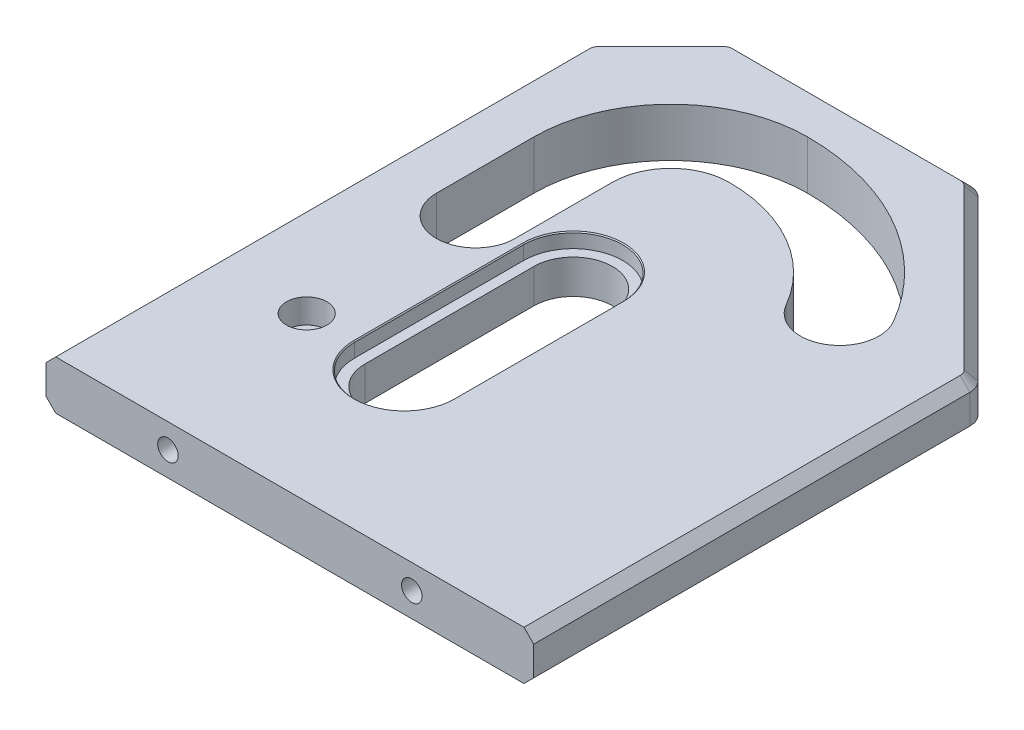
SolidWorks part; units mm, degrees
ref_plane "Front Plane" through (0, 0, 0) normal (0, 0, 1) x (1, 0, 0)
ref_plane "Top Plane" through (0, 0, 0) normal (0, 1, 0) x (1, 0, 0)
ref_plane "Right Plane" through (0, 0, 0) normal (1, 0, 0) x (0, 0, -1)
sketch "Sketch1" plane through (0, 0, 0) normal (0, 1, 0) x (1, 0, 0)
  line L1 (-40, -68.0944) -> (60, -68.0944)
  line L2 (-40, -68.0944) -> (-40, 58)
  line L3 (-40, 58) -> (60, 58)
  line L4 (60, -68.0944) -> (60, 58)
  dimension "D1" = 68.0944
  dimension "D2" = 40
  dimension "D3" = 58
  dimension "D4" = 60
extrude "Boss-Extrude1" add sketch "Sketch1" along normal mid plane 10
sketch "Slots Path" plane through (0, 0, 0) normal (0, 1, 0) x (1, 0, 0)
  line L2 (-20, 0) -> (-20, 20)
  line L3 (0, 0) -> (0, -34.641)
  line L4 (-5.5, 0) -> (5.5, 0) construction
  arc A1 (0, 40) -> (-20, 20) centre (0, 20) ccw
  arc A2 (0, 40) -> (34.641, 20) centre (0, 0) cw
  point P1 (-20, -34.641)
  dimension "D1" = 20
  dimension "D2" = 40
  dimension "D3" = 20
  dimension "D4" = 20
  dimension "D5" = 40
sketch "Sketch3" plane through (0, 5, 0) normal (0, 1, 0) x (1, 0, 0)
  line L9 (-8.05, 0) -> (-8.05, -34.641)
  line L10 (-11.95, 0) -> (-11.95, 20)
  line L11 (-28.05, 0) -> (-28.05, 20)
  line L12 (8.05, 0) -> (8.05, -34.641)
  arc A2 (-8.05, 0) -> (8.05, 0) centre (0, 0) cw
  arc A3 (-8.05, -34.641) -> (8.05, -34.641) centre (0, -34.641) ccw
  arc A18 (0, 31.95) -> (-11.95, 20) centre (0, 20) ccw
  arc A19 (27.6695, 15.975) -> (0, 31.95) centre (0, 0) ccw
  arc A20 (0, 48.05) -> (-28.05, 20) centre (0, 20) ccw
  arc A21 (41.6125, 24.025) -> (0, 48.05) centre (0, 0) ccw
  arc A22 (-11.95, 0) -> (-28.05, 0) centre (-20, 0) cw
  arc A23 (27.6695, 15.975) -> (41.6125, 24.025) centre (34.641, 20) ccw
extrude "Slots" cut sketch "Sketch3" against normal through all
sketch "Sketch11" plane through (0, 5, 0) normal (0, 1, 0) x (1, 0, 0)
  line L4 (-10.15, 0) -> (-10.15, -34.641)
  line L5 (10.15, 0) -> (10.15, -34.641)
  arc A2 (-10.15, 0) -> (10.15, 0) centre (0, 0) cw
  arc A3 (-10.15, -34.641) -> (10.15, -34.641) centre (0, -34.641) ccw
extrude "Cut-Extrude5" cut sketch "Sketch11" against normal blind 3
chamfer "Chamfer2" distance 0.2 angle 45 4 edges at (0, 5, 44.791) (10.15, 5, 17.3205) (0, 5, -10.15) (-10.15, 5, 17.3205)
hole_wizard "M5x0.8 Tapped Hole2" positions "Sketch8" profile "Sketch9" tap size "M5x0.8" standard "ANSI Metric" end condition through all
sketch "Sketch8" plane through (0, 5, 0) normal (0, 1, 0) x (1, 0, 0)
  point P0 (-20, -34.641)
cosmetic thread "Hole Thread3" parameters "D2"=5
sketch "Sketch9" plane through (-20, 5, 34.641) normal (1, 0, 0) x (0, 0, 1)
  line L0 (0, 0) -> (0, 10)
  line L1 (0, 10) -> (2.1, 10)
  line L2 (2.1, 10) -> (2.1, 0)
  line L5 (2.1, 0) -> (0, 0)
  line L11 (0, -6.35) -> (0, 107.95) construction
  dimension "Thru Tap Drill Dia." = 4.2
  dimension "Thru Tap Drill Depth" = 10
sketch "Sketch10" plane through (0, 5, 0) normal (0, 1, 0) x (1, 0, 0)
  circle A0 centre (-20, -34.641) radius 4.15
extrude "Cut-Extrude4" cut sketch "Sketch10" against normal blind 5
hole_wizard "M5x0.8 Tapped Hole1" positions "Sketch6" profile "Sketch7" tap size "M5x0.8" standard "ANSI Metric"
sketch "Sketch6" plane through (0, 0, 68.0944) normal (0, 0, 1) x (1, 0, 0)
  line L0 (55, 0) -> (-55, 0) construction
  line L1 (-40, 5) -> (-40, -5) construction
  line L2 (60, 5) -> (60, -5) construction
  point P0 (-15, 0)
  point P2 (35, 0)
  point P11 (-40, 0)
  dimension "D1" = 25
  dimension "D2" = 25
sketch "Sketch7" plane through (-15, 0, 68.0944) normal (1, 0, 0) x (0, -1, 0)
  line L0 (0, 0) -> (0, 21.2618)
  line L1 (0, 21.2618) -> (2.1, 20)
  line L2 (2.1, 20) -> (2.1, 0)
  line L5 (2.1, 0) -> (0, 0)
  line L10 (0, 21.2618) -> (-2.1, 20) construction
  line L11 (0, -6.35) -> (0, 107.95) construction
  dimension "Tap Drill Dia." = 4.2
  dimension "Tap Drill Depth" = 20
  dimension "Drill Angle" = 118
cosmetic thread "Hole Thread1" parameters "D1"=20, "D2"=5
cosmetic thread "Hole Thread2" parameters "D1"=20, "D2"=5
sketch "Sketch4" plane through (0, 5, 0) normal (0, 1, 0) x (1, 0, 0)
  line L0 (-40, 43) -> (-40, 58)
  line L1 (-40, 58) -> (-40, -68.0944) construction
  line L2 (-40, 58) -> (-25, 58)
  line L3 (60, 58) -> (-40, 58) construction
  line L4 (-25, 58) -> (-40, 43)
  dimension "D1" = 15
  dimension "D2" = 15
extrude "Cut-Extrude2" cut sketch "Sketch4" against normal through all
sketch "Sketch5" plane through (0, 5, 0) normal (0, 1, 0) x (1, 0, 0)
  line L0 (25, 58) -> (60, 58)
  line L1 (60, 58) -> (-25, 58) construction
  line L2 (60, 58) -> (60, 23)
  line L3 (60, -68.0944) -> (60, 58) construction
  line L4 (60, 23) -> (25, 58)
  dimension "D1" = 35
  dimension "D2" = 35
extrude "Cut-Extrude3" cut sketch "Sketch5" against normal through all
fillet "Fillet1" radius 4 4 edges at (60, 0, -23) (25, 0, -58) (-25, 0, -58) (-40, 0, -43)
chamfer "Chamfer1" distance 2 angle 45 18 edges at (60, -5, 23.3756) (42.5, -5, -40.5) (0, -5, -58) (-32.5, -5, -50.5) (-40, -5, 13.3756) (60, 5, 23.3756) (42.5, 5, -40.5) (0, 5, -58) (-32.5, 5, -50.5) (-40, 5, 13.3756) (59.6955, -5, -22.8739) (24.8739, -5, -57.6955) (-24.8739, -5, -57.6955) (-39.6955, -5, -42.8739) (59.6955, 5, -22.8739) (24.8739, 5, -57.6955) (-24.8739, 5, -57.6955) (-39.6955, 5, -42.8739)
